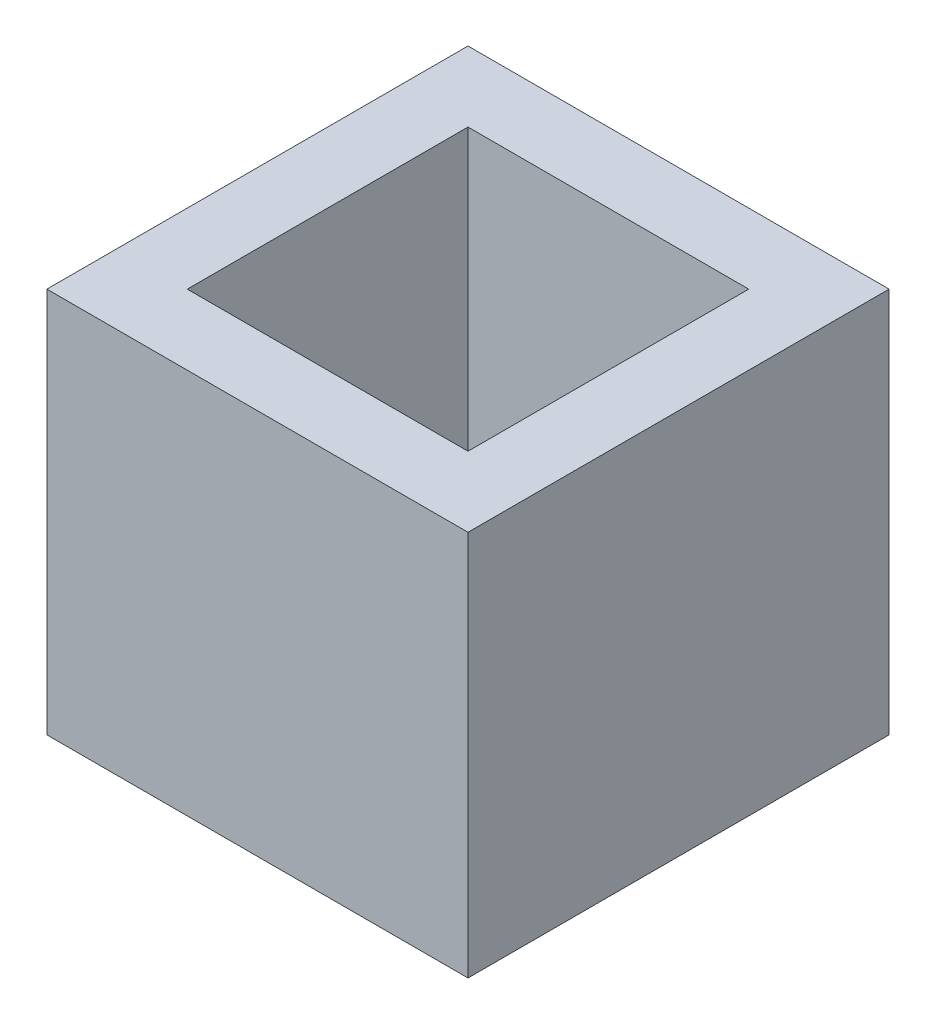
SolidWorks part; units mm, degrees
ref_plane "Front Plane" through (0, 0, 0) normal (0, 0, 1) x (1, 0, 0)
ref_plane "Top Plane" through (0, 0, 0) normal (0, 1, 0) x (1, 0, 0)
ref_plane "Right Plane" through (0, 0, 0) normal (1, 0, 0) x (0, 0, -1)
sketch "Sketch1" plane through (0, 0, 0) normal (0, 1, 0) x (1, 0, 0)
  line L1 (0, 0) -> (12, 0)
  line L2 (0, 0) -> (0, 12)
  line L3 (0, 12) -> (12, 12)
  line L4 (12, 0) -> (12, 12)
  dimension "D1" = 12
  dimension "D2" = 12
extrude "Boss-Extrude1" add sketch "Sketch1" along normal blind 11
shell "Shell1" thickness 2
sketch "Sketch2" plane through (0, 2, 0) normal (0, 1, 0) x (1, 0, 0)
  line L0 (12, 0) -> (12, 12) construction
  line L1 (12, 12) -> (0, 12) construction
  circle A0 centre (6, 6) radius 3
  point P0 (6, 6)
  dimension "D3" = 6
  dimension "D1" = 6
  dimension "D2" = 6
sketch "Sketch3" plane through (0, 0, 0) normal (0, -1, 0) x (1, 0, 0)
  circle A0 centre (6, -4.73) radius 0.625
  circle A1 centre (6, -7.27) radius 0.625
  point P0 (6, -4.73)
  point P1 (6, -7.27)
  dimension "D1" = 1.25
  dimension "D2" = 1.25
extrude "Cut-Extrude1" cut sketch "Sketch3" against normal blind 10
